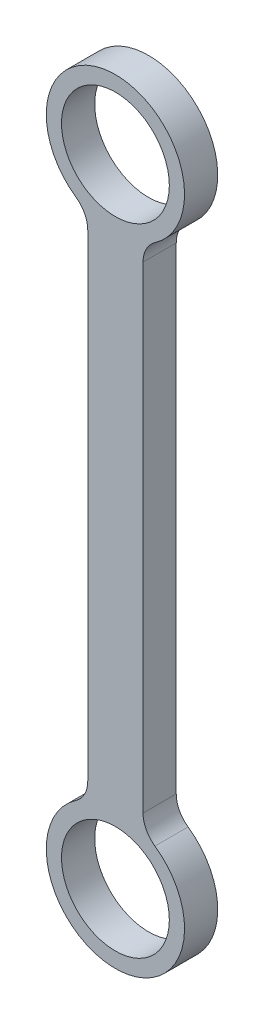
SolidWorks part; units mm, degrees
ref_plane "Alzado" through (0, 0, 0) normal (0, 0, 1) x (1, 0, 0)
ref_plane "Planta" through (0, 0, 0) normal (0, 1, 0) x (1, 0, 0)
ref_plane "Vista lateral" through (0, 0, 0) normal (1, 0, 0) x (0, 0, -1)
sketch "Croquis1" plane through (0, 0, 0) normal (0, 0, 1) x (1, 0, 0)
  line L0 (0, 0) -> (0, 115) construction
  line L2 (5, 0) -> (-5, 0)
  line L3 (5, 0) -> (5, 115)
  line L4 (5, 115) -> (-5, 115)
  line L5 (-5, 0) -> (-5, 115)
  line L6 (5, 0) -> (-5, 115) construction
  line L7 (5, 115) -> (-5, 0) construction
  circle A0 centre (0, 0) radius 12.5
  circle A1 centre (0, 0) radius 9.75
  circle A2 centre (0, 115) radius 12.5
  circle A3 centre (0, 115) radius 9.75
  point P7 (0, 57.5)
  dimension "D1" = 25
  dimension "D2" = 19.5
  dimension "D3" = 25
  dimension "D4" = 19.5
  dimension "D5" = 115
  dimension "D6" = 115
  dimension "D7" = 10
extrude "Saliente-Extruir1" add sketch "Croquis1" along normal blind 6 contours A3 L3 A2 L5 | A3 L5 A2 L3 | A2 L5 A0 L3 | A1 L5 A0 L3 | A1 L3 A0 L5
fillet "Redondeo1" radius 5 4 edges at (5, 11.4564, 3) (-5, 11.4564, 3) (-5, 103.5436, 3) (5, 103.5436, 3)
